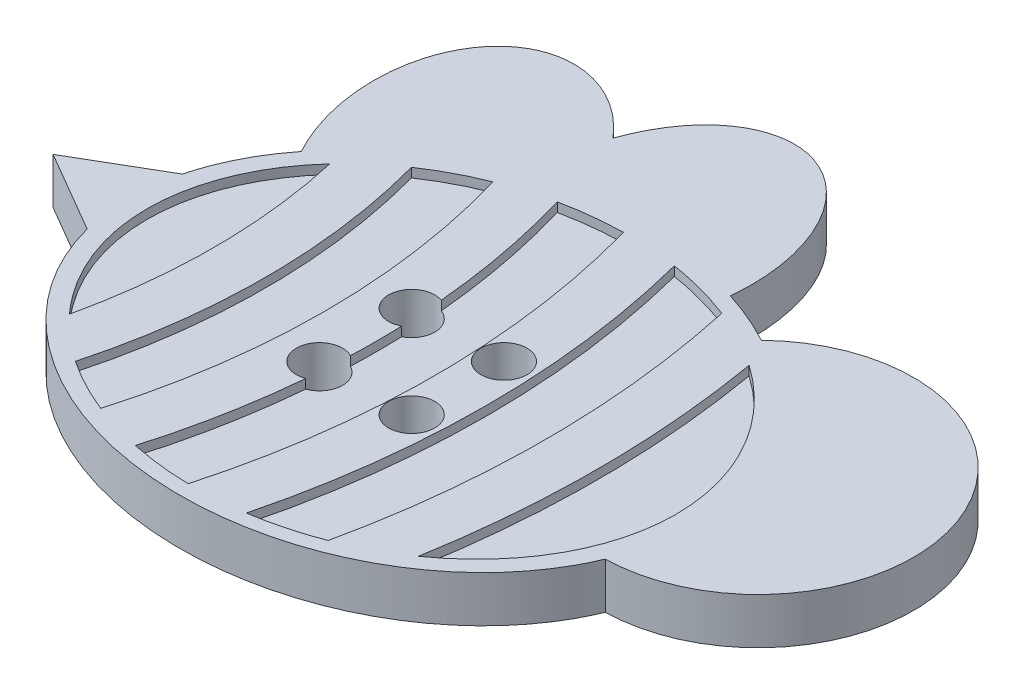
SolidWorks part; units mm, degrees
ref_plane "Front Plane" through (0, 0, 0) normal (0, 0, 1) x (1, 0, 0)
ref_plane "Top Plane" through (0, 0, 0) normal (0, 1, 0) x (1, 0, 0)
ref_plane "Right Plane" through (0, 0, 0) normal (1, 0, 0) x (0, 0, -1)
sketch "Sketch1" plane through (0, 0, 0) normal (0, 1, 0) x (1, 0, 0)
  line L0 (-55, 0) -> (55, 0) construction
  line L1 (-9.5284, 1.6393) -> (-12.3408, 0)
  line L2 (-9.5284, -1.6393) -> (-12.3408, 0)
  arc A2 (9.2223, -2.5578) -> (5.3861, 6.6476) centre (9.1169, 2.8003) ccw
  ellipse E0 centre (0, 0) end of major axis (9.736, 0) minor radius 7.98 (-9.5284, -1.6393) -> (9.2223, -2.5578) ccw
  ellipse E1 centre (-5.3002, 6.6939) end of major axis (-3.7555, 1.8503) minor radius 3.5621 (-3.1888, 10.1186) -> (-8.1574, 4.3561) ccw
  ellipse E2 centre (0, 7.98) end of major axis (-0.2051, 2.9002) minor radius 3.5621 (3.532, 7.4363) -> (-3.1888, 10.1186) ccw
  ellipse E3 centre (0, 0) end of major axis (9.736, 0) minor radius 7.98 (5.3861, 6.6476) -> (3.532, 7.4363) ccw
  ellipse E4 centre (0, 0) end of major axis (9.736, 0) minor radius 7.98 (-8.1574, 4.3561) -> (-9.5284, 1.6393) ccw
extrude "Boss-Extrude1" add sketch "Sketch1" along normal blind 1.5875
sketch "Sketch2" plane through (0, 1.5875, 0) normal (0, 1, 0) x (1, 0, 0)
  line L1 (-55, 0) -> (55, 0) construction
  line L6 (0, 0) -> (-9.1055, 0) construction
  arc A6 (-7.2987, -4.48) -> (-7.2987, 4.48) centre (-27.1187, 0) ccw
  arc A7 (-5.7907, -5.7825) -> (-5.7907, 5.7825) centre (-27.1187, 0) ccw
  arc A8 (-3.9521, -6.7503) -> (-3.9521, 6.7503) centre (-27.1187, 0) ccw
  arc A9 (-2.2489, -7.2608) -> (-2.2489, 7.2608) centre (-27.1187, 0) ccw
  arc A10 (-0.2017, -7.4911) -> (-0.2017, 7.4911) centre (-27.1187, 0) ccw
  arc A11 (1.6721, -7.3655) -> (1.6721, 7.3655) centre (-27.1187, 0) ccw
  arc A12 (3.901, -6.7704) -> (3.901, 6.7704) centre (-27.1187, 0) ccw
  arc A13 (5.9227, -5.6912) -> (5.9227, 5.6912) centre (-27.1187, 0) ccw
  ellipse E4 centre (0, 0) end of major axis (9.1055, 0) minor radius 7.4929 (-5.7907, -5.7825) -> (-3.9521, -6.7503) ccw
  ellipse E5 centre (0, 0) end of major axis (9.1055, 0) minor radius 7.4929 (-7.2987, 4.48) -> (-7.2987, -4.48) ccw
  ellipse E6 centre (0, 0) end of major axis (9.1055, 0) minor radius 7.4929 (-3.9521, 6.7503) -> (-5.7907, 5.7825) ccw
  ellipse E7 centre (0, 0) end of major axis (9.1055, 0) minor radius 7.4929 (-2.2489, -7.2608) -> (-0.2017, -7.4911) ccw
  ellipse E8 centre (0, 0) end of major axis (9.1055, 0) minor radius 7.4929 (1.6721, -7.3655) -> (3.901, -6.7704) ccw
  ellipse E9 centre (0, 0) end of major axis (9.1055, 0) minor radius 7.4929 (-0.2017, 7.4911) -> (-2.2489, 7.2608) ccw
  ellipse E10 centre (0, 0) end of major axis (9.1055, 0) minor radius 7.4929 (5.9227, -5.6912) -> (5.9227, 5.6912) ccw
  ellipse E11 centre (0, 0) end of major axis (9.1055, 0) minor radius 7.4929 (3.901, 6.7704) -> (1.6721, 7.3655) ccw
extrude "Cut-Extrude1" cut sketch "Sketch2" against normal blind 0.3175
sketch "Sketch3" plane through (0, 1.5875, 0) normal (0, 1, 0) x (1, 0, 0)
  line L5 (0, -0.8731) -> (0, 0.8731) construction
  line L6 (-0.8731, 0) -> (0.8731, 0) construction
  circle A0 centre (-1.5875, 1.5875) radius 0.7938
  circle A1 centre (1.5875, 1.5875) radius 0.7938
  circle A2 centre (1.5875, -1.5875) radius 0.7938
  circle A3 centre (-1.5875, -1.5875) radius 0.7938
  point P0 (0, 0)
extrude "Cut-Extrude2" cut sketch "Sketch3" against normal through all and the other way through all
